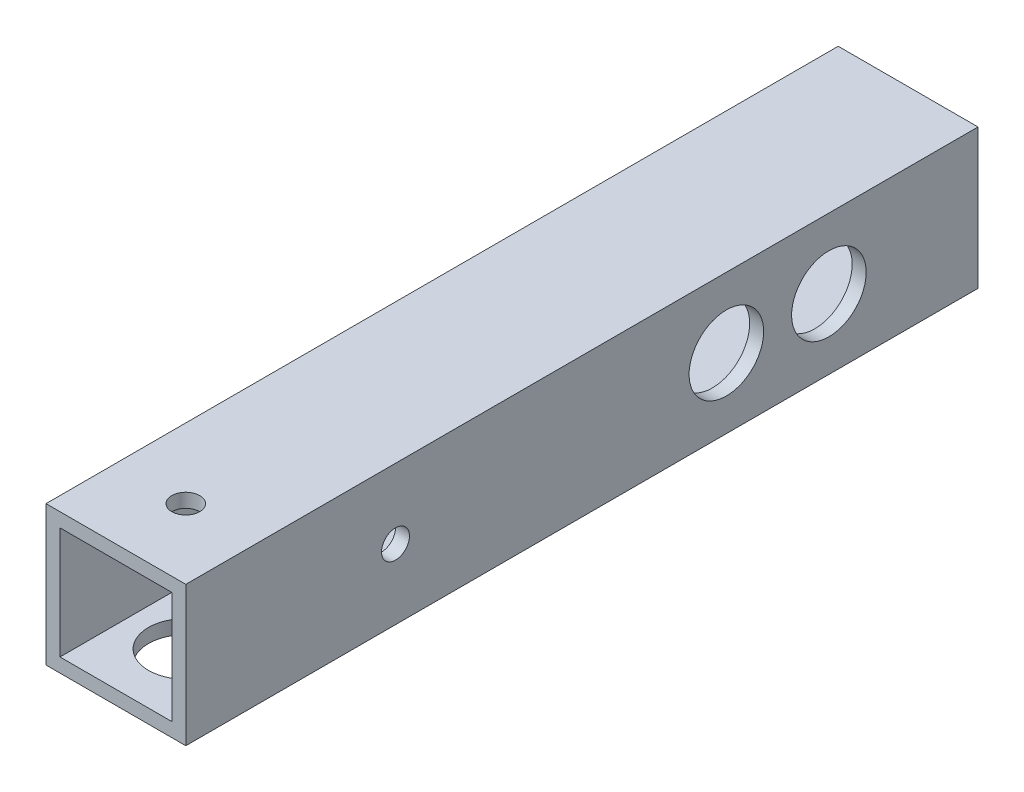
SolidWorks part; units mm, degrees
material "1060 合金"
ref_plane "正面" through (0, 0, 0) normal (0, 0, 1) x (1, 0, 0)
ref_plane "平面" through (0, 0, 0) normal (0, 1, 0) x (1, 0, 0)
ref_plane "右側面" through (0, 0, 0) normal (1, 0, 0) x (0, 0, -1)
sketch "ｽｹｯﾁ1" plane through (0, 0, 0) normal (0, 0, 1) x (1, 0, 0)
  line L1 (-7.0101, 7.7326) -> (7.9899, 7.7326)
  line L2 (-7.0101, 7.7326) -> (-7.0101, -7.2674)
  line L3 (-7.0101, -7.2674) -> (7.9899, -7.2674)
  line L4 (7.9899, 7.7326) -> (7.9899, -7.2674)
  line L9 (-5.5101, 6.2326) -> (6.4899, 6.2326)
  line L10 (-5.5101, 6.2326) -> (-5.5101, -5.7674)
  line L11 (-5.5101, -5.7674) -> (6.4899, -5.7674)
  line L12 (6.4899, 6.2326) -> (6.4899, -5.7674)
  dimension "D1" = 15
  dimension "D2" = 15
  dimension "D3" = 1.5
  dimension "D4" = 1.5
  dimension "D5" = 12
  dimension "D6" = 12
extrude "ﾎﾞｽ - 押し出し2" add sketch "ｽｹｯﾁ1" along normal blind 85
sketch "ｽｹｯﾁ3" plane through (0, 7.7326, 0) normal (0, 1, 0) x (1, 0, 0)
  line L0 (7.9899, -85) -> (-7.0101, -85) construction
  circle A0 centre (0.4899, -77.5) radius 1.5
  dimension "D1" = 7.5
extrude "ｶｯﾄ - 押し出し2" cut sketch "ｽｹｯﾁ3" against normal blind 10
sketch "ｽｹｯﾁ4" plane through (7.9899, 0, 0) normal (1, 0, 0) x (0, 0, -1)
  line L0 (-85, -7.2674) -> (-85, 7.7326) construction
  circle A0 centre (-62.5, 0.2326) radius 1.5
  dimension "D1" = 22.5
extrude "ｶｯﾄ - 押し出し3" cut sketch "ｽｹｯﾁ4" against normal blind 10
sketch "ｽｹｯﾁ5" plane through (0, -7.2674, 0) normal (0, -1, 0) x (1, 0, 0)
  circle A0 centre (0.4899, 77.5) radius 4
  circle A1 centre (0.4899, 77.5) radius 1.5 construction
extrude "ｶｯﾄ - 押し出し4" cut sketch "ｽｹｯﾁ5" against normal blind 10
sketch "ｽｹｯﾁ6" plane through (-7.0101, 0, 0) normal (-1, 0, 0) x (0, 0, 1)
  circle A0 centre (62.5, 0.2326) radius 4
  circle A1 centre (62.5, 0.2326) radius 1.5 construction
extrude "ｶｯﾄ - 押し出し5" cut sketch "ｽｹｯﾁ6" against normal blind 10
sketch "ｽｹｯﾁ7" plane through (-7.0101, 0, 0) normal (-1, 0, 0) x (0, 0, 1)
  line L0 (0, 7.7326) -> (0, -7.2674) construction
  circle A0 centre (16, 0.2326) radius 3
  dimension "D1" = 16
extrude "ｶｯﾄ - 押し出し6" cut sketch "ｽｹｯﾁ7" against normal blind 10
sketch "ｽｹｯﾁ8" plane through (-7.0101, 0, 0) normal (-1, 0, 0) x (0, 0, 1)
  line L1 (85, 7.7326) -> (0, 7.7326) construction
  circle A0 centre (5, 0.2326) radius 1.5
  circle A1 centre (16, 0.2326) radius 3 construction
  dimension "D1" = 11
  dimension "D2" = 7.5
extrude "ｶｯﾄ - 押し出し7" cut sketch "ｽｹｯﾁ8" against normal blind 10
sketch "ｽｹｯﾁ9" plane through (-7.0101, 0, 0) normal (-1, 0, 0) x (0, 0, 1)
  circle A0 centre (27, 0.2326) radius 1.5
  circle A1 centre (16, 0.2326) radius 3 construction
  dimension "D1" = 11
extrude "ｶｯﾄ - 押し出し8" cut sketch "ｽｹｯﾁ9" against normal blind 10
sketch "ｽｹｯﾁ10" plane through (7.9899, 0, 0) normal (1, 0, 0) x (0, 0, -1)
  circle A0 centre (-16, 0.2326) radius 4
  circle A1 centre (-27, 0.2326) radius 4
  circle A6 centre (-27, 0.2326) radius 1.5 construction
  circle A7 centre (-16, 0.2326) radius 3 construction
extrude "ｶｯﾄ - 押し出し9" cut sketch "ｽｹｯﾁ10" against normal blind 10
